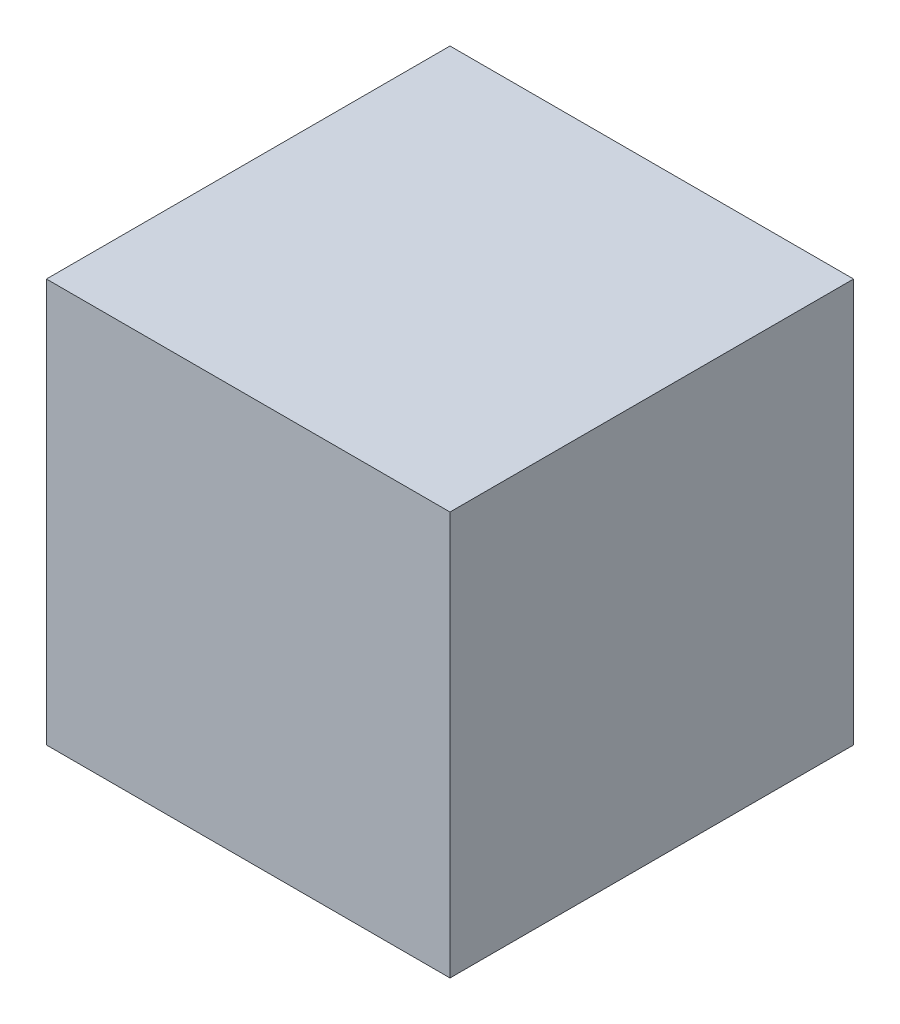
SolidWorks part; units mm, degrees
ref_plane "Front Plane" through (0, 0, 0) normal (0, 0, 1) x (1, 0, 0)
ref_plane "Top Plane" through (0, 0, 0) normal (0, 1, 0) x (1, 0, 0)
ref_plane "Right Plane" through (0, 0, 0) normal (1, 0, 0) x (0, 0, -1)
sketch "Sketch1" plane through (0, 0, 0) normal (0, 1, 0) x (1, 0, 0)
  line L1 (-150, 150) -> (150, 150)
  line L2 (-150, 150) -> (-150, -150)
  line L3 (-150, -150) -> (150, -150)
  line L4 (150, 150) -> (150, -150)
  line L5 (-150, 150) -> (150, -150) construction
  line L6 (-150, -150) -> (150, 150) construction
  point P0 (0, 0)
  dimension "D1" = 300
  dimension "D2" = 300
extrude "Boss-Extrude1" add sketch "Sketch1" along normal blind 300
